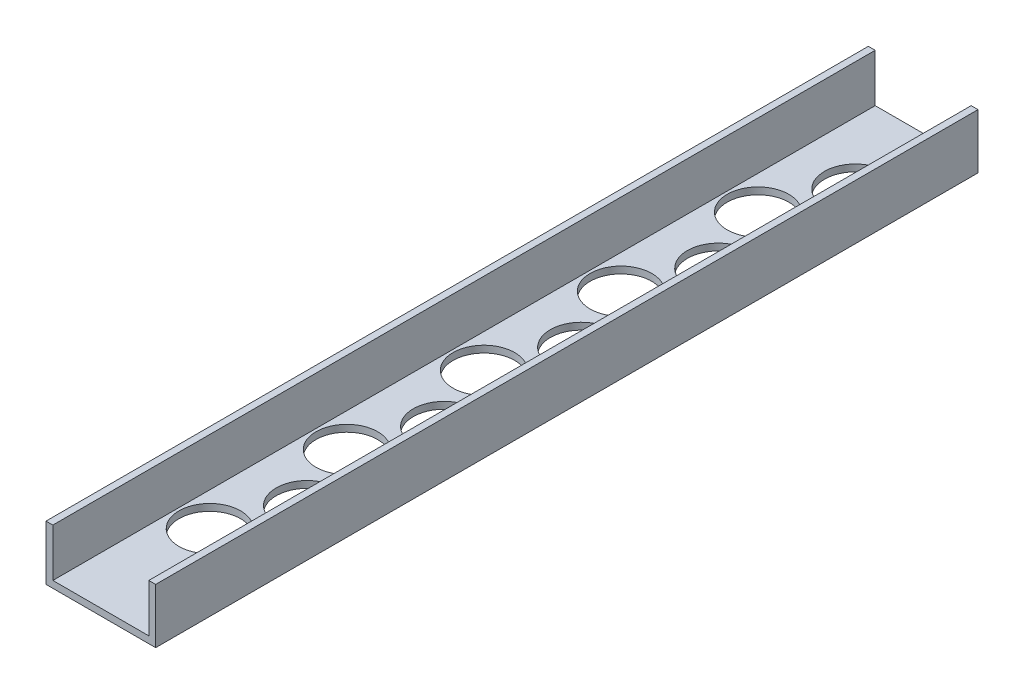
SolidWorks part; units mm, degrees
material "6063-T6"
ref_plane "Front" through (0, 0, 0) normal (0, 0, 1) x (1, 0, 0)
ref_plane "Top" through (0, 0, 0) normal (0, 1, 0) x (1, 0, 0)
ref_plane "Right" through (0, 0, 0) normal (1, 0, 0) x (0, 0, -1)
sketch "Sketch1" plane through (0, 0, 0) normal (0, 0, 1) x (1, 0, 0)
  line L0 (3.175, 3.175) -> (3.175, 25.4)
  line L1 (0, 0) -> (50.8, 0)
  line L2 (0, 0) -> (0, 25.4)
  line L4 (50.8, 0) -> (50.8, 25.4)
  line L5 (3.175, 3.175) -> (47.625, 3.175)
  line L6 (47.625, 3.175) -> (47.625, 25.4)
  line L7 (0, 25.4) -> (3.175, 25.4)
  line L8 (50.8, 25.4) -> (47.625, 25.4)
  dimension "D1" = 25.4
  dimension "D2" = 50.8
  dimension "D3" = 3.175
extrude "Boss-Extrude1" add sketch "Sketch1" along normal blind 381
sketch "Sketch2" plane through (0, 3.175, 0) normal (0, 1, 0) x (1, 0, 0)
  line L0 (46.355, -38.1) -> (47.625, -38.1) construction
  line L1 (47.625, -381) -> (47.625, 0) construction
  line L2 (4.445, -69.85) -> (3.175, -69.85) construction
  line L3 (3.175, -381) -> (3.175, 0) construction
  line L4 (32.0675, -38.1) -> (32.0675, 0) construction
  line L5 (47.625, 0) -> (3.175, 0) construction
  line L6 (18.7325, -69.85) -> (18.7325, 0) construction
  circle A0 centre (32.0675, -38.1) radius 14.2875
  circle A1 centre (18.7325, -69.85) radius 14.2875
  circle A2 centre (18.7325, -133.35) radius 14.2875
  circle A3 centre (32.0675, -101.6) radius 14.2875
  circle A4 centre (18.7325, -196.85) radius 14.2875
  circle A5 centre (32.0675, -165.1) radius 14.2875
  circle A6 centre (18.7325, -260.35) radius 14.2875
  circle A7 centre (32.0675, -228.6) radius 14.2875
  circle A8 centre (18.7325, -323.85) radius 14.2875
  circle A9 centre (32.0675, -292.1) radius 14.2875
  dimension "D1" = 28.575
  dimension "D2" = 28.575
  dimension "D3" = 5
  dimension "D4" = 38.1
  dimension "D5" = 69.85
extrude "Cut-Extrude1" cut sketch "Sketch2" against normal up to next
